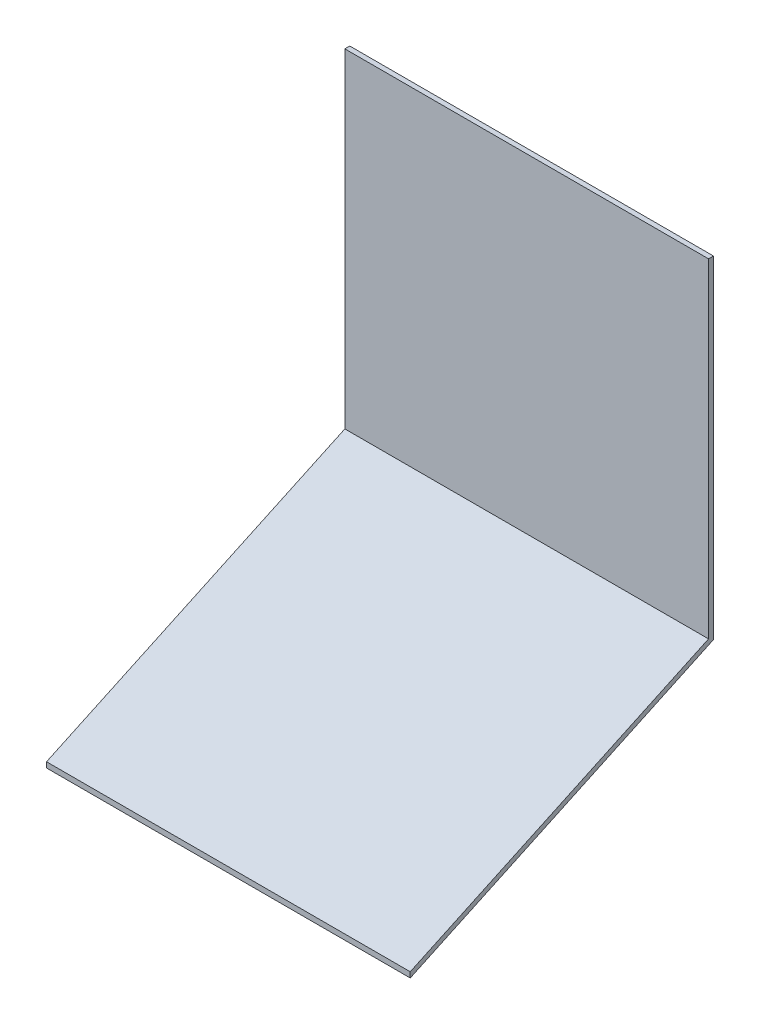
SolidWorks part; units mm, degrees
material "Plain Carbon Steel"
ref_plane "Front Plane" through (0, 0, 0) normal (0, 0, 1) x (1, 0, 0)
ref_plane "Top Plane" through (0, 0, 0) normal (0, 1, 0) x (1, 0, 0)
ref_plane "Right Plane" through (0, 0, 0) normal (1, 0, 0) x (0, 0, -1)
sketch "Sketch1" plane through (0, 0, 0) normal (1, 0, 0) x (0, 0, -1)
  line L0 (0, 0) -> (92.0809, 42.938)
  line L1 (92.0809, 42.938) -> (92.0809, 144.538)
  line L2 (92.0809, 144.538) -> (93.5998, 144.538)
  line L3 (93.5998, 144.538) -> (93.5998, 41.9704)
  line L4 (93.5998, 41.9704) -> (0, -1.6759)
  line L5 (0, -1.6759) -> (0, 0)
  dimension "D1" = 1.5189
  dimension "D2" = 1.5189
  dimension "D3" = 101.6
  dimension "D4" = 101.6
  dimension "D5" = 115
extrude "Boss-Extrude1" add sketch "Sketch1" along normal blind 112.268
